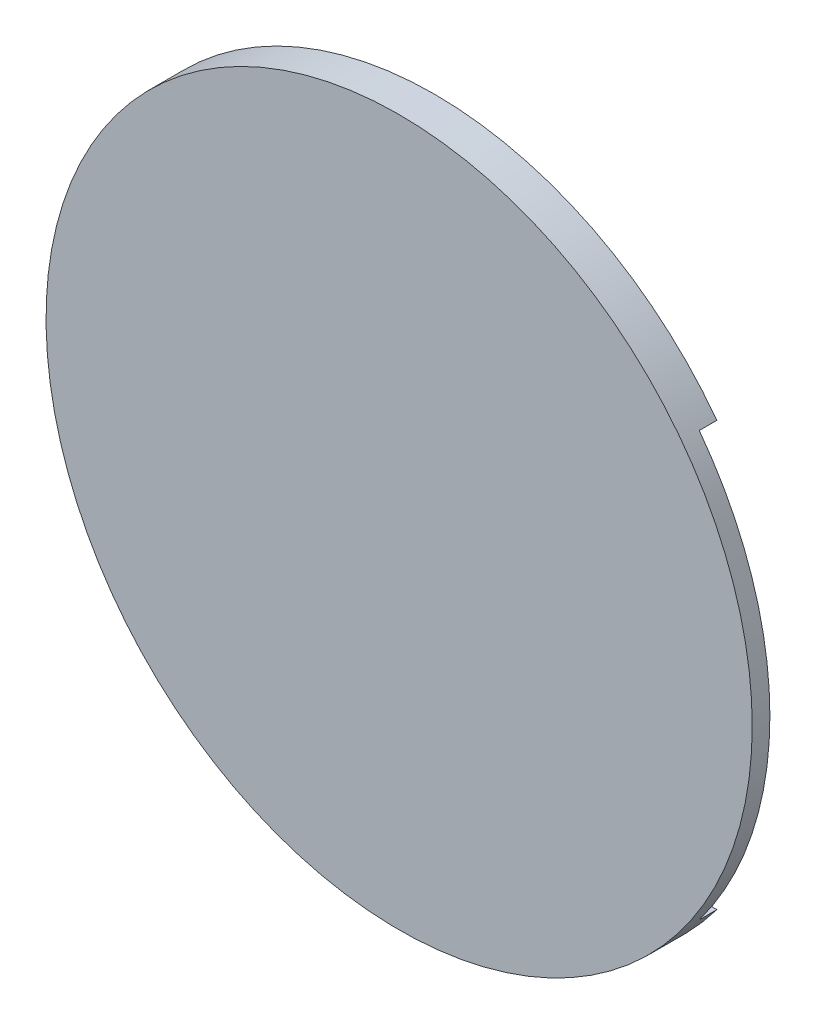
SolidWorks part; units mm, degrees
material "ABS"
ref_plane "Front Plane" through (0, 0, 0) normal (0, 0, 1) x (1, 0, 0)
ref_plane "Top Plane" through (0, 0, 0) normal (0, 1, 0) x (1, 0, 0)
ref_plane "Right Plane" through (0, 0, 0) normal (1, 0, 0) x (0, 0, -1)
sketch "Sketch1" plane through (0, 0, 0) normal (0, 0, 1) x (1, 0, 0)
  circle A0 centre (0, 0) radius 31.75
extrude "Base" add sketch "Sketch1" along normal mid plane 3.175
sketch "Sketch5" plane through (0, 0, 0) normal (1, 0, 0) x (0, 0, -1)
  line L0 (1.5875, -31.75) -> (1.5875, 31.75) construction
  line L1 (1.5875, 19.05) -> (1.5875, -19.05)
  line L3 (1.5875, 19.05) -> (0, 19.05)
  line L4 (1.5875, 19.05) -> (1.5875, -19.05)
  line L5 (1.5875, -19.05) -> (0, -19.05)
  line L6 (0, 19.05) -> (0, -19.05)
  arc A0 (1.5875, 19.05) -> (1.5875, -19.05) centre (115.0938, 0) ccw
  point P3 (0, 0)
  point P9 (0, 0)
  point P10 (0, 0)
  dimension "D1" = 38.1
extrude "Trench" cut sketch "Sketch5" against normal mid plane 63.5 contours A0 L6 L5 | A0 L3 L6 | L1 A0
